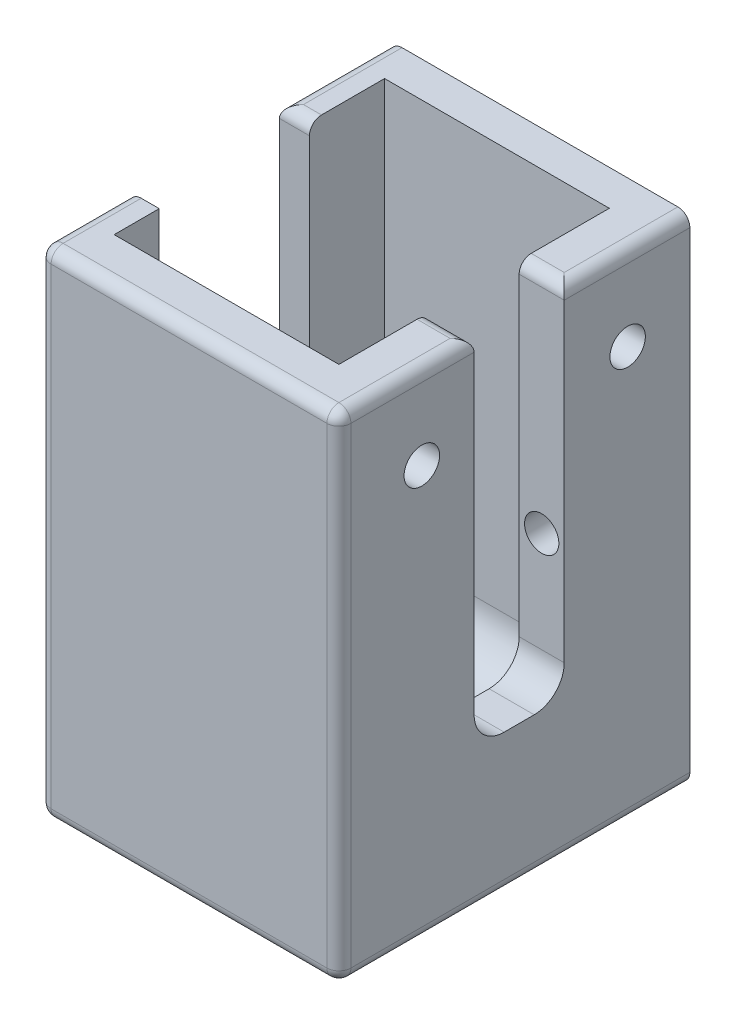
SolidWorks part; units mm, degrees
ref_plane "Front Plane" through (0, 0, 0) normal (0, 0, 1) x (1, 0, 0)
ref_plane "Top Plane" through (0, 0, 0) normal (0, 1, 0) x (1, 0, 0)
ref_plane "Right Plane" through (0, 0, 0) normal (1, 0, 0) x (0, 0, -1)
sketch "Sketch2" plane through (0, 0, 0) normal (0, 1, 0) x (1, 0, 0)
  line L0 (-9.5, -11.43) -> (9.5, -11.43)
  line L5 (12.04, -14.43) -> (-13.31, -14.43)
  line L10 (-13.31, -14.43) -> (-13.31, 15.24)
  line L15 (-13.31, 15.24) -> (12.04, 15.24)
  line L16 (12.04, 15.24) -> (12.04, 7.62)
  line L17 (12.04, -14.43) -> (12.04, -5.08)
  line L18 (12.04, 7.62) -> (9.5, 7.62)
  line L19 (9.5, 7.62) -> (9.5, 11.43)
  line L20 (9.5, 11.43) -> (-9.5, 11.43)
  line L21 (-9.5, 11.43) -> (-9.5, -11.43)
  line L22 (12.04, -5.08) -> (9.5, -5.08)
  line L24 (9.5, -11.43) -> (9.5, -5.08)
  point P6 (0, 11.43)
  point P12 (-9.5, 0)
  dimension "D1" = 22.86
  dimension "D2" = 19
  dimension "D3" = 3.81
  dimension "D4" = 3.81
  dimension "D5" = 7.62
  dimension "D6" = 2.54
  dimension "D7" = 5.08
  dimension "D8" = 3
extrude "Boss-Extrude2" add sketch "Sketch2" along normal blind 38.1
sketch "Sketch1" plane through (0, 0, 0) normal (0, 1, 0) x (1, 0, 0)
  line L1 (-13.31, -14.43) -> (12.04, -14.43)
  line L2 (-13.31, -14.43) -> (-13.31, 15.24)
  line L3 (-13.31, 15.24) -> (12.04, 15.24)
  line L4 (12.04, -14.43) -> (12.04, 15.24)
  point P0 (0, 0)
extrude "Boss-Extrude3" add sketch "Sketch1" against normal blind 3.81
sketch "Sketch3" plane through (0, 0, 0) normal (0, 1, 0) x (1, 0, 0)
  line L1 (-1.88, -3.81) -> (1.12, -3.81)
  line L2 (-1.88, -3.81) -> (-1.88, 3.81)
  line L3 (-1.88, 3.81) -> (1.12, 3.81)
  line L4 (1.12, -3.81) -> (1.12, 3.81)
  line L5 (-9.5, -11.43) -> (-9.5, 11.43) construction
  point P6 (-1.88, 0)
  dimension "D1" = 7.62
  dimension "D2" = 3
  dimension "D3" = 7.62
extrude "Cut-Extrude1" cut sketch "Sketch3" against normal through all
sketch "Sketch4" plane through (-9.5, 0, 0) normal (1, 0, 0) x (0, 0, -1)
  line L0 (-11.43, 38.1) -> (11.43, 38.1) construction
  line L1 (-3.81, 38.1) -> (3.81, 38.1)
  line L2 (-3.81, 38.1) -> (-3.81, 8)
  line L3 (-3.81, 8) -> (3.81, 8)
  line L4 (3.81, 38.1) -> (3.81, 8)
  line L5 (-11.43, 0) -> (11.43, 0) construction
  line L6 (-11.43, 38.1) -> (11.43, 38.1) construction
  point P10 (0, 38.1)
  point P11 (0, 38.1)
  dimension "D1" = 8
  dimension "D2" = 7.62
extrude "Cut-Extrude2" cut sketch "Sketch4" against normal through all
sketch "Sketch5" plane through (-9.5, 0, 0) normal (1, 0, 0) x (0, 0, -1)
  line L1 (-11.43, 0) -> (11.43, 0) construction
  circle A0 centre (-9.17, 31) radius 1.5
  circle A1 centre (8.23, 31) radius 1.5
  dimension "D3" = 3
  dimension "D1" = 2.26
  dimension "D2" = 17.4
  dimension "D4" = 31
extrude "Cut-Extrude3" cut sketch "Sketch5" against normal through all
sketch "Sketch6" plane through (0, 0, 14.43) normal (0, 0, 1) x (1, 0, 0)
  line L0 (-13.31, 38.1) -> (-13.31, -3.81) construction
  line L3 (-1.88, -3.81) -> (-1.88, 0) construction
  line L8 (12.04, 38.1) -> (12.04, 0) construction
  line L11 (-13.31, 38.1) -> (-9.5, 38.1) construction
  circle A0 centre (-11.405, 19.05) radius 1.45
  circle A1 centre (-3.81, -1.905) radius 1.45
  point P9 (-1.88, -1.905)
  point P20 (-11.405, 38.1)
  point P26 (12.04, 19.05)
  dimension "D1" = 2.9
  dimension "D2" = 9.5
extrude "Cut-Extrude4" cut sketch "Sketch6" against normal offset from surface (24.844 mm away) 6.604 up to face at (-11.405, 23.05, -3.81) offset beyond the face yes
fillet "Fillet1" radius 4 2 edges at (0, 0, -11.43) (0, 0, 11.43)
mirror "Mirror1" about plane through (0, 0, 0) normal (0, 0, 1) of bodies 106 120
delete or keep bodies "Body-Delete/Keep 1" type keep bodies bodies 116
fillet "Fillet4" radius 2.54 2 edges at (-11.405, 8, -3.81) (-11.405, 8, 3.81)
fillet "Fillet2" radius 1.016 11 edges at (-13.31, 17.145, 15.24) (12.04, 17.145, 15.24) (12.04, -3.81, 0.405) (-13.31, -3.81, 0.405) (-0.635, -3.81, 15.24) (12.04, 38.1, 11.43) (-0.635, 38.1, 15.24) (-13.31, 38.1, 9.525) (-13.31, 38.1, -9.12) (-11.405, 38.1, -3.81) (-11.405, 38.1, 3.81)
fillet "Fillet3" radius 1.27 4 edges at (-0.38, 0, -3.81) (-1.88, 0, 0) (-0.38, 0, 3.81) (1.12, 0, 0)
fillet "Fillet5" radius 1.016 2 edges at (12.04, 38.1, -9.755) (10.77, 38.1, -5.08)
ref_plane "Plane1" through (-15.85, 0, 0) normal (-1, 0, 0) x (0, 0, 1)
mirror "Mirror3" about plane through (-15.85, 0, 0) normal (-1, 0, 0) of bodies 116 117 121
sketch "Sketch7" plane through (0, 0, 0) normal (0, 1, 0) x (1, 0, 0)
  line L0 (11.5383, -3.9427) -> (11.5383, 17.9144) construction
  text T0 "Lt\r\n" font "Century Gothic" height in points 28
extrude "Cut-Extrude5" cut sketch "Sketch7" against normal blind 1.27
sketch "Sketch8" plane through (0, 0, 0) normal (0, 1, 0) x (1, 0, 0)
  line L0 (-42.724, -6.0799) -> (-42.724, 4.0801) construction
  line L1 (-42.724, -14.224) -> (-42.724, -7.62) construction
  text T0 "Rt\r\n" font "Century Gothic" height in points 28
  dimension "D1" = 10.16
extrude "Cut-Extrude6" cut sketch "Sketch8" against normal blind 1.27
delete or keep bodies "Body-Delete/Keep 2" type delete bodies bodies 117
equation "\".30.83in\"=0.83"
